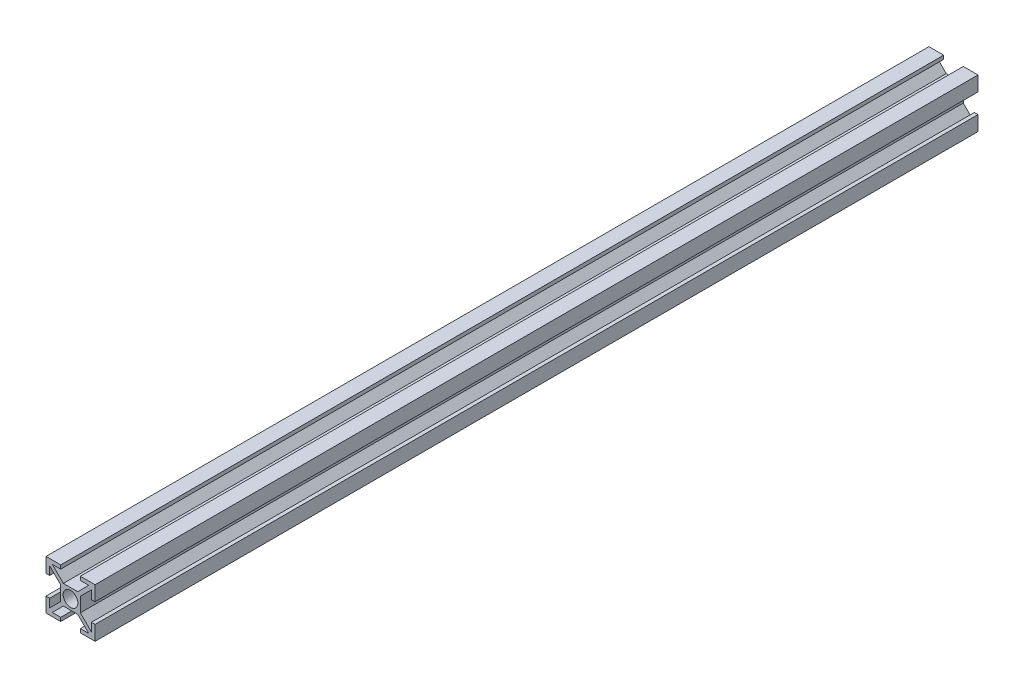
SolidWorks part; units mm, degrees
material "3.0205 (EN-AW 1200)"
ref_plane "Plano frontal" through (0, 0, 0) normal (0, 0, 1) x (1, 0, 0)
ref_plane "Plano superior" through (0, 0, 0) normal (0, 1, 0) x (1, 0, 0)
ref_plane "Plano direito" through (0, 0, 0) normal (1, 0, 0) x (0, 0, -1)
sketch "Esboço1" plane through (0, 0, 0) normal (0, 0, 1) x (1, 0, 0)
  line L0 (-2.9393, 4) -> (2.9393, 4)
  line L1 (-10, -10) -> (-4, -10)
  line L2 (-10, -10) -> (-10, -4)
  line L3 (-10, 10) -> (-4, 10)
  line L4 (10, -10) -> (10, -4)
  line L5 (-10, -10) -> (-4, -4) construction
  line L6 (-10, 10) -> (0, 0) construction
  line L7 (-7.4393, -8.5) -> (-2.9393, -4)
  line L8 (4, -10) -> (10, -10)
  line L9 (-8.5, -7.4393) -> (-4, -2.9393)
  line L10 (-8.5, 7.4393) -> (-4, 2.9393)
  line L11 (-7.4393, -8.5) -> (-4, -8.5)
  line L12 (-8.5, -7.4393) -> (-8.5, -4)
  line L13 (-7.4393, 8.5) -> (-4, 8.5)
  line L14 (8.5, -7.4393) -> (8.5, -4)
  line L17 (-4, 10) -> (-4, 8.5)
  line L18 (4, -8.5) -> (7.4393, -8.5)
  line L19 (-10, -4) -> (-8.5, -4)
  line L20 (4, 10) -> (4, 8.5)
  line L21 (-10, 4) -> (-8.5, 4)
  line L22 (-4, 2.9393) -> (-4, -2.9393)
  line L23 (-4, -8.5) -> (-4, -10)
  line L24 (-8.5, 4) -> (-8.5, 7.4393)
  line L25 (-10, 4) -> (-10, 10)
  line L26 (-7.4393, 8.5) -> (-2.9393, 4)
  line L27 (4, 8.5) -> (7.4393, 8.5)
  line L28 (-2.9393, -4) -> (2.9393, -4)
  line L29 (4, 10) -> (10, 10)
  line L30 (4, -8.5) -> (4, -10)
  line L31 (10, 4) -> (10, 10)
  line L32 (8.5, 4) -> (8.5, 7.4393)
  line L33 (-10.5303, -9.4697) -> (9.4697, 10.5303) construction
  line L34 (8.5, 4) -> (10, 4)
  line L35 (8.5, -4) -> (10, -4)
  line L36 (-10, -10) -> (10, 10) construction
  line L37 (4, 2.9393) -> (4, -2.9393)
  line L38 (-9.4697, -10.5303) -> (10.5303, 9.4697) construction
  line L40 (2.9393, -4) -> (7.4393, -8.5)
  line L41 (4, -4) -> (10, -10) construction
  line L43 (4, -2.9393) -> (8.5, -7.4393)
  line L44 (4, 0) -> (10, 0) construction
  line L45 (4, 2.9393) -> (8.5, 7.4393)
  line L47 (4, 4) -> (10, 10) construction
  line L48 (2.9393, 4) -> (7.4393, 8.5)
  circle A0 centre (0, 0) radius 3
  point P0 (0, 0)
  point P14 (-4.0323, -3.9672)
  dimension "D5" = 6
  dimension "D1" = 0.75
  dimension "D3" = 1.5
  dimension "D4" = 20
  dimension "D6" = 8
  dimension "D7" = 20
  dimension "D9" = 1.5
  dimension "D2" = 8
extrude "Ressalto-extrusão1" add sketch "Esboço1" along normal blind 360
